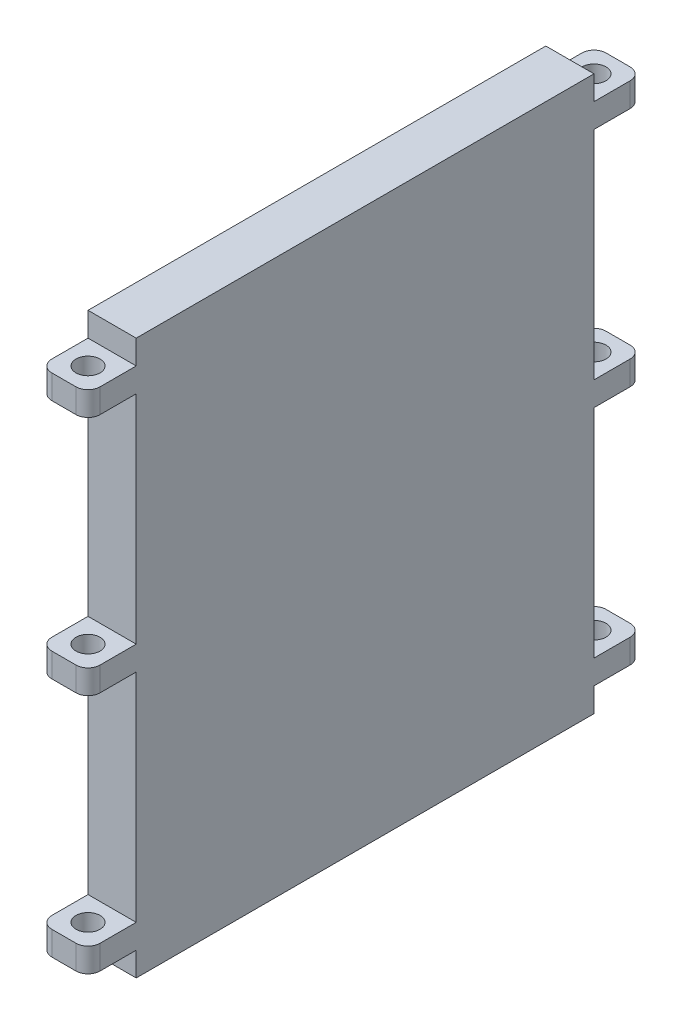
SolidWorks part; units mm, degrees
ref_plane "Front Plane" through (0, 0, 0) normal (0, 0, 1) x (1, 0, 0)
ref_plane "Top Plane" through (0, 0, 0) normal (0, 1, 0) x (1, 0, 0)
ref_plane "Right Plane" through (0, 0, 0) normal (1, 0, 0) x (0, 0, -1)
sketch "Sketch1" plane through (0, 0, 0) normal (1, 0, 0) x (0, 0, -1)
  line L1 (-115, 115) -> (115, 115)
  line L2 (-115, 115) -> (-115, -115)
  line L3 (-115, -115) -> (115, -115)
  line L4 (115, 115) -> (115, -115)
  line L5 (-115, 115) -> (115, -115) construction
  line L6 (-115, -115) -> (115, 115) construction
  point P0 (0, 0)
  dimension "D1" = 230
  dimension "D2" = 230
extrude "Boss-Extrude1" add sketch "Sketch1" along normal blind 20
sketch "Sketch2" plane through (0, 0, 115) normal (0, 0, 1) x (1, 0, 0)
  line L0 (20, 115) -> (20, -115) construction
  line L1 (0, 115) -> (20, 115)
  line L2 (0, 115) -> (0, 105)
  line L3 (0, 105) -> (20, 105)
  line L4 (20, 115) -> (20, 105)
  line L5 (0, 115) -> (0, -115) construction
  line L6 (0, 95) -> (20, 95)
  line L7 (0, 95) -> (0, 5)
  line L8 (0, 5) -> (20, 5)
  line L9 (20, 95) -> (20, 5)
  line L11 (0, -5) -> (20, -5)
  line L12 (0, -5) -> (0, -95)
  line L13 (0, -95) -> (20, -95)
  line L14 (20, -5) -> (20, -95)
  line L15 (0, -115) -> (20, -115)
  line L16 (0, -115) -> (0, -105)
  line L17 (0, -105) -> (20, -105)
  line L18 (20, -115) -> (20, -105)
  dimension "D1" = 10
  dimension "D2" = 90
  dimension "D3" = 10
  dimension "D4" = 10
  dimension "D5" = 10
  dimension "D6" = 90
extrude "Cut-Extrude1" cut sketch "Sketch2" against normal blind 20
sketch "Sketch3" plane through (0, 105, 0) normal (0, 1, 0) x (1, 0, 0)
  line L0 (0, -95) -> (0, -115) construction
  line L1 (0, -115) -> (20, -115) construction
  circle A0 centre (10, -105) radius 5
  dimension "D1" = 10
  dimension "D2" = 10
  dimension "D3" = 10
extrude "Cut-Extrude2" cut sketch "Sketch3" against normal up to surface (210 mm away) up to face at (10, -105, 105)
fillet "Fillet1" radius 5 6 edges at (20, -100, 115) (0, -100, 115) (20, 0, 115) (0, 0, 115) (20, 100, 115) (0, 100, 115)
mirror "Mirror5" about plane through (0, 0, 0) normal (0, 0, 1) of "Cut-Extrude2", "Cut-Extrude1"
fillet "Fillet2" radius 5 6 edges at (0, -100, -115) (20, -100, -115) (0, 0, -115) (20, 0, -115) (0, 100, -115) (20, 100, -115)
